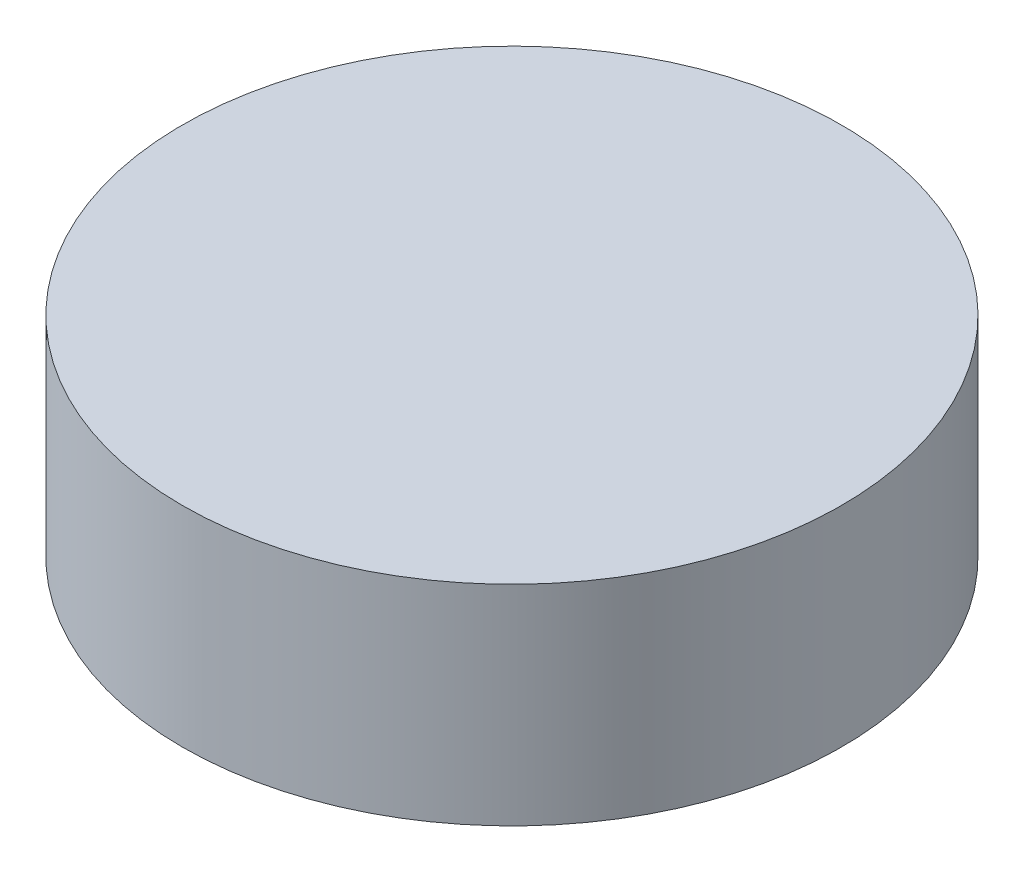
SolidWorks part; units mm, degrees
ref_plane "Front Plane" through (0, 0, 0) normal (0, 0, 1) x (1, 0, 0)
ref_plane "Top Plane" through (0, 0, 0) normal (0, 1, 0) x (1, 0, 0)
ref_plane "Right Plane" through (0, 0, 0) normal (1, 0, 0) x (0, 0, -1)
sketch "Sketch1" plane through (0, 0, 0) normal (0, 1, 0) x (1, 0, 0)
  circle A0 centre (0, 0) radius 5
extrude "Boss-Extrude1" add sketch "Sketch1" along normal blind 3.175 contours A0
